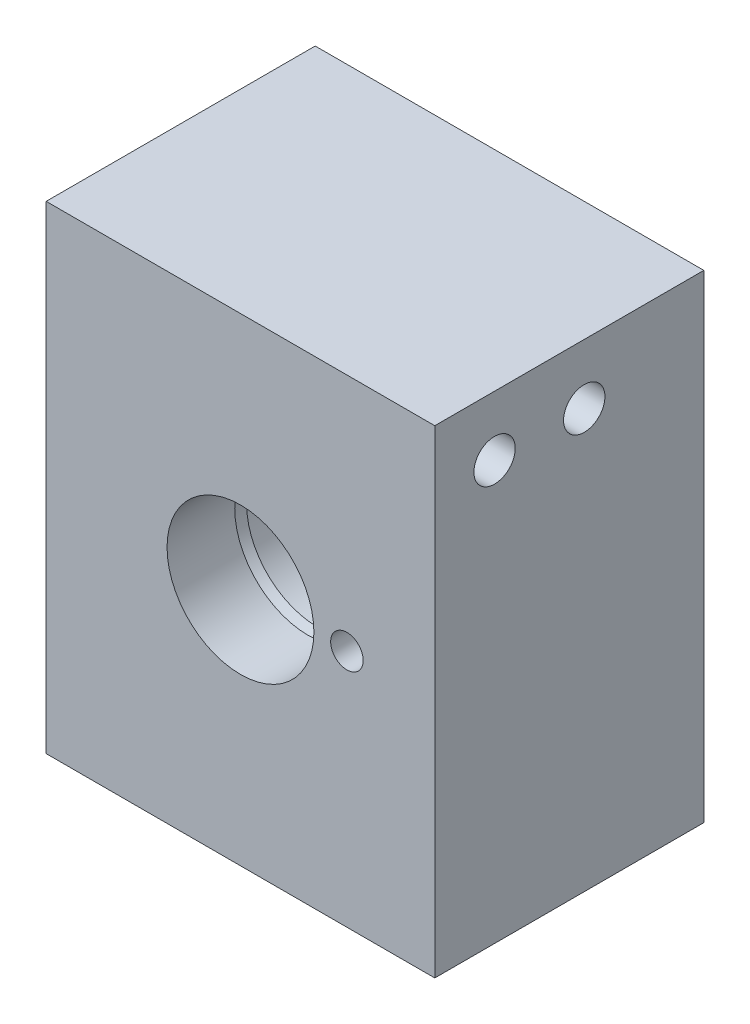
SolidWorks part; units mm, degrees
material "6061-T6 (SS)"
ref_plane "Front Plane" through (0, 0, 0) normal (0, 0, 1) x (1, 0, 0)
ref_plane "Top Plane" through (0, 0, 0) normal (0, 1, 0) x (1, 0, 0)
ref_plane "Right Plane" through (0, 0, 0) normal (1, 0, 0) x (0, 0, -1)
sketch "Sketch7" plane through (0, 0, 0) normal (0, 1, 0) x (1, 0, 0)
  line L0 (-22.225, 6.35) -> (19.05, 6.35)
  line L1 (19.05, 6.35) -> (19.05, -22.225)
  line L2 (19.05, -22.225) -> (-22.225, -22.225)
  line L6 (-22.225, 6.35) -> (-22.225, -22.225)
  dimension "D2" = 41.275
  dimension "D3" = 28.575
extrude "Boss-Extrude2" add sketch "Sketch7" along normal blind 50.8
sketch "Sketch31" plane through (0, 0, -6.35) normal (0, 0, -1) x (-1, 0, 0)
  line L0 (1.5875, 25.4) -> (1.5875, 0) construction
  line L1 (-19.05, 0) -> (22.225, 0) construction
  line L2 (1.5875, 25.4) -> (22.225, 25.4) construction
  line L3 (22.225, 50.8) -> (22.225, 0) construction
  circle A0 centre (1.5875, 25.4) radius 9.525
  dimension "D1" = 19.05
extrude "Cut-Extrude1" cut sketch "Sketch31" against normal blind 6.35
sketch "Sketch22" plane through (0, 0, 22.225) normal (0, 0, 1) x (1, 0, 0)
  line L0 (-22.225, 0) -> (19.05, 0) construction
  line L1 (-1.5875, 0) -> (-1.5875, 50.8) construction
  line L3 (-22.225, 50.8) -> (19.05, 50.8) construction
  point P0 (-1.5875, 25.4)
sketch "Sketch23" plane through (0, 0, -6.35) normal (0, 0, -1) x (-1, 0, 0)
  point P0 (1.5875, 25.4)
curve "Curve3"
sketch3d "3DSketch6"
  line L0 (-1.5875, 25.4, 22.225) -> (-1.5875, 25.4, -6.35) construction
sketch "Sketch24" plane through (-1.5875, 0, 0) normal (-1, 0, 0) x (0, 0, 1)
  line L0 (22.225, 25.4) -> (22.225, 33.1978)
  line L1 (22.225, 33.1978) -> (15.0368, 33.1978)
  line L2 (15.0368, 33.1978) -> (14.0415, 32.9311)
  line L3 (14.0415, 32.9311) -> (8.2804, 32.9311)
  line L4 (8.0772, 32.7279) -> (8.0772, 29.2735)
  line L5 (7.6373, 29.0195) -> (4.7752, 29.0195)
  line L6 (4.572, 28.8163) -> (4.572, 26.034)
  line L7 (4.572, 26.034) -> (3.1116, 26.049)
  line L8 (3.1116, 26.049) -> (-0.715, 28.2582)
  line L9 (-0.715, 28.2582) -> (-0.715, 25.4)
  line L10 (-0.715, 25.4) -> (22.225, 25.4)
  line L11 (8.0772, 29.2735) -> (7.6373, 29.0195)
  arc A0 (8.2804, 32.9311) -> (8.0772, 32.7279) centre (8.2804, 32.7279) ccw
  arc A1 (4.7752, 29.0195) -> (4.572, 28.8163) centre (4.7752, 28.8163) ccw
  dimension "D3" = 0.2032
  dimension "D9" = 0.2032
  dimension "D1" = 7.7978
  dimension "D2" = 7.5311
  dimension "D4" = 7.1882
  dimension "D5" = 15
  dimension "D6" = 14.1478
  dimension "D7" = 30
  dimension "D8" = 3.6195
  dimension "D10" = 17.653
  dimension "D11" = 1.4605
  dimension "D12" = 0.586
  dimension "D13" = 30
  dimension "D14" = 0.649
  dimension "D16" = 0.254
revolve "Port Manifold" cut sketch "Sketch24" angle 360 about L10
fillet "Fillet3" radius 0.127 1 edges at (-2.2215, 25.4, 4.572)
hole_wizard "#8-32 Tapped Hole1" positions "Sketch26" profile "Sketch27" tap size "#8-32" standard "ANSI Inch"
sketch "Sketch26" plane through (0, 0, 22.225) normal (0, 0, 1) x (1, 0, 0)
  line L0 (-1.5875, 25.4) -> (9.7155, 25.4) construction
  line L2 (-1.5875, 25.4) -> (-1.5875, 14.097) construction
  circle A0 centre (-1.5875, 25.4) radius 11.303
  point P0 (9.7155, 25.4)
  dimension "D1" = 22.606
sketch "Sketch27" plane through (9.7155, 25.4, 22.225) normal (1, 0, 0) x (0, -1, 0)
  line L0 (0, 0) -> (0, 11.1978)
  line L1 (0, 11.1978) -> (1.7272, 10.16)
  line L2 (1.7272, 10.16) -> (1.7272, 0)
  line L5 (1.7272, 0) -> (0, 0)
  line L10 (0, 11.1978) -> (-1.7272, 10.16) construction
  line L11 (0, -6.35) -> (0, 107.95) construction
  dimension "Tap Drill Dia." = 3.4544
  dimension "Tap Drill Depth" = 10.16
  dimension "Drill Angle" = 118
cosmetic thread "Hole Thread1" parameters "D1"=8.382, "D2"=4.1656
hole_wizard "1/8 NPT Tapped Hole1" positions "Sketch28" profile "Sketch29" size "1/8" standard "ANSI Inch"
sketch "Sketch28" plane through (0, 0, 0) normal (0, -1, 0) x (-1, 0, 0)
  line L0 (1.5875, -7.9375) -> (1.5875, -22.225) construction
  line L1 (22.225, -22.225) -> (-19.05, -22.225) construction
  point P0 (1.5875, -7.9375)
  dimension "D1" = 14.2875
cosmetic thread "Hole Thread2" parameters "D1"=6.858, "D2"=10.2827
sketch "Sketch29" plane through (-1.5875, 0, 7.9375) normal (1, 0, 0) x (0, 0, -1)
  line L0 (0, 0) -> (0, 14.2175)
  line L1 (4.2164, 11.684) -> (0, 14.2175)
  line L2 (-4.2164, 11.684) -> (0, 14.2175) construction
  line L3 (4.2164, 11.684) -> (4.2164, 6.858)
  line L4 (4.2164, 6.858) -> (4.5374, 6.858)
  line L5 (4.5374, 6.858) -> (4.7427, 0)
  line L6 (-4.5374, 6.858) -> (-4.7427, 0) construction
  line L7 (4.7427, 0) -> (0, 0)
  line L8 (0, -6.35) -> (0, 107.95) construction
  line L11 (-4.2164, 6.858) -> (-4.5374, 6.858) construction
  dimension "Tap Drill Dia." = 8.4328
  dimension "Tap Drill Depth" = 11.684
  dimension "Thread Dia." = 9.4855
  dimension "Thread Angle" = 3.43
  dimension "Thread Depth" = 6.858
  dimension "Drill Angle" = 118
hole_wizard "#17 (0.173) Diameter Hole1" positions "Sketch37" profile "Sketch38" hole size "#17" standard "ANSI Inch" end condition through all
sketch "Sketch37" plane through (-22.225, 0, 0) normal (-1, 0, 0) x (0, 0, 1)
  line L0 (15.875, 44.45) -> (6.35, 44.45) construction
  line L2 (-6.35, 50.8) -> (22.225, 50.8) construction
  line L3 (11.1125, 53.975) -> (11.1125, 44.45) construction
  line L5 (22.225, 50.8) -> (22.225, 0) construction
  point P0 (6.35, 44.45)
  point P2 (15.875, 44.45)
  dimension "D1" = 6.35
  dimension "D2" = 9.525
  dimension "D3" = 6.35
sketch "Sketch38" plane through (-22.225, 44.45, 6.35) normal (0, 1, 0) x (0, 0, 1)
  line L0 (0, 0) -> (0, 41.275)
  line L1 (0, 41.275) -> (2.1971, 41.275)
  line L2 (2.1971, 41.275) -> (2.1971, 0)
  line L5 (2.1971, 0) -> (0, 0)
  line L11 (0, -6.35) -> (0, 107.95) construction
  dimension "Thru Hole Dia." = 4.3942
  dimension "Thru Hole Depth" = 41.275
hole_wizard "#46 (0.081) Diameter Hole1" positions "Sketch39" profile "Sketch40" hole size "#46" standard "ANSI Inch"
sketch "Sketch39" plane through (0, 0, 0) normal (0, -1, 0) x (-1, 0, 0)
  point P0 (1.5875, -7.9375)
sketch "Sketch40" plane through (-1.5875, 0, 7.9375) normal (1, 0, 0) x (0, 0, -1)
  line L0 (0, 0) -> (0, 19.685)
  line L1 (0, 19.685) -> (1.0287, 19.0669)
  line L2 (1.0287, 19.0669) -> (1.0287, 0)
  line L5 (1.0287, 0) -> (0, 0)
  line L10 (0, 19.685) -> (-1.0287, 19.0669) construction
  line L11 (0, -6.35) -> (0, 107.95) construction
  dimension "Hole Dia." = 2.0574
  dimension "Hole Depth" = 19.685
  dimension "Drill Angle" = 118
